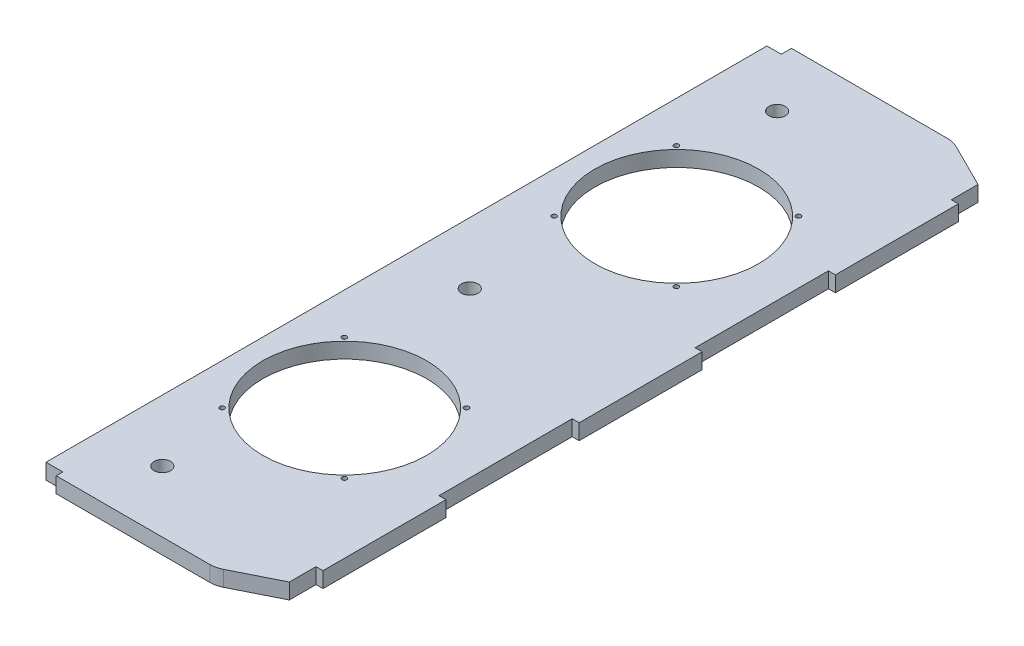
SolidWorks part; units mm, degrees
material "PE High Density"
ref_plane "Front Plane" through (0, 0, 0) normal (0, 0, 1) x (1, 0, 0)
ref_plane "Top Plane" through (0, 0, 0) normal (0, 1, 0) x (1, 0, 0)
ref_plane "Right Plane" through (0, 0, 0) normal (1, 0, 0) x (0, 0, -1)
sketch "Sketch1" plane through (0, 0, 0) normal (0, 1, 0) x (1, 0, 0)
  line L0 (0, 0) -> (0, 457.2)
  line L1 (0, 457.2) -> (139.7, 457.2)
  line L10 (139.7, 457.2) -> (139.7, 0)
  line L11 (139.7, 0) -> (0, 0)
  line L12 (0, 228.6) -> (139.7, 228.6) construction
  circle A0 centre (63.5, 125.73) radius 50.8
  circle A1 centre (38.1, 38.1) radius 5.08
  circle A3 centre (38.1, 419.1) radius 5.08
  circle A4 centre (63.5, 331.47) radius 50.8
  circle A5 centre (38.1, 228.6) radius 5.08
  dimension "D11" = 10.16
  dimension "D17" = 10.16
  dimension "D3" = 101.6
  dimension "D4" = 10.16
  dimension "D7" = 82.55
  dimension "D2" = 63.5
  dimension "Length of Rib" = 457.2
  dimension "D5" = 38.1
  dimension "D6" = 190.5
  dimension "D12" = 38.1
  dimension "D13" = 38.1
  dimension "D18" = 38.1
  dimension "D19" = 38.1
  dimension "Width of Rib" = 139.7
extrude "Boss-Extrude1" add sketch "Sketch1" along normal blind 9.652
sketch "Sketch4" plane through (0, 9.652, 0) normal (0, 1, 0) x (1, 0, 0)
  line L0 (10.4524, -8.5852) -> (10.4524, -21.2852) construction
  line L1 (0, 0) -> (10.4524, 0)
  line L2 (0, 0) -> (0, 4.1148)
  line L3 (0, 4.1148) -> (10.4524, 4.1148)
  line L4 (10.4524, 0) -> (10.4524, 4.1148)
  line L6 (0, 457.2) -> (8.8649, 457.2)
  line L7 (0, 457.2) -> (0, 450.85)
  line L8 (0, 450.85) -> (8.8649, 450.85)
  line L9 (8.8649, 457.2) -> (8.8649, 450.85)
extrude "Cut-Extrude1" cut sketch "Sketch4" against normal through all
chamfer "Chamfer1" distance 15.24 distance2 30.48 1 edges at (139.7, 4.826, -457.2)
chamfer "Chamfer2" distance 30.48 distance2 15.24 1 edges at (139.7, 4.826, 0)
fillet "Fillet2" radius 15.24 2 edges at (109.22, 4.826, -457.2) (109.22, 4.826, 0)
sketch "Sketch5" plane through (139.7, 0, 0) normal (1, 0, 0) x (0, 0, -1)
  line L0 (15.24, 9.652) -> (441.96, 9.652) construction
  line L1 (31.75, 9.652) -> (107.95, 9.652)
  line L2 (31.75, 9.652) -> (31.75, 0)
  line L3 (31.75, 0) -> (107.95, 0)
  line L4 (107.95, 9.652) -> (107.95, 0)
  line L5 (15.24, 0) -> (441.96, 0) construction
  line L6 (0, 0) -> (0, 9.652) construction
  line L7 (190.5, 9.652) -> (190.5, 0)
  line L8 (190.5, 9.652) -> (266.7, 9.652)
  line L9 (190.5, 0) -> (266.7, 0)
  line L10 (266.7, 9.652) -> (266.7, 0)
  line L11 (349.25, 9.652) -> (349.25, 0)
  line L12 (349.25, 9.652) -> (425.45, 9.652)
  line L13 (349.25, 0) -> (425.45, 0)
  line L14 (425.45, 9.652) -> (425.45, 0)
  dimension "D1" = 31.75
  dimension "D2" = 76.2
  dimension "D3" = 3
extrude "Boss-Extrude2" add sketch "Sketch5" along normal blind 4.318
sketch "Sketch7" plane through (0, 9.652, 0) normal (0, 1, 0) x (1, 0, 0)
  line L0 (10.4524, 0) -> (105.6223, 0) construction
  line L1 (139.7, 107.95) -> (139.7, 190.5) construction
  line L2 (101.092, 87.884) -> (101.092, 163.576) construction
  line L4 (101.092, 87.884) -> (25.4, 87.884) construction
  line L5 (25.4, 87.884) -> (25.4, 163.576) construction
  line L6 (25.4, 163.576) -> (101.092, 163.576) construction
  point P0 (101.092, 87.884)
  point P2 (25.4, 87.884)
  point P4 (25.4, 163.576)
  point P6 (101.092, 163.576)
  dimension "D1" = 87.884
  dimension "D2" = 38.608
  dimension "D3" = 75.692
  dimension "D4" = 75.692
  dimension "D5" = 75.692
  dimension "D6" = 75.692
hole_wizard "Ø3.0 (3) Diameter Hole1" positions "Sketch7" profile "Sketch8" hole size "Ø3.0" standard "ANSI Metric" end condition up to next
sketch "Sketch8" plane through (101.092, 9.652, -87.884) normal (1, 0, 0) x (0, 0, 1)
  line L0 (0, 0) -> (0, 9.652)
  line L1 (0, 9.652) -> (1.5, 9.652)
  line L2 (1.5, 9.652) -> (1.5, 0)
  line L5 (1.5, 0) -> (0, 0)
  line L11 (0, -6.35) -> (0, 107.95) construction
  dimension "Thru Hole Dia." = 3
  dimension "Thru Hole Depth" = 9.652
sketch "Sketch9" plane through (0, 9.652, 0) normal (0, 1, 0) x (1, 0, 0)
  line L0 (144.018, 228.6) -> (-0.0043, 228.6) construction
  line L1 (144.018, 266.7) -> (144.018, 190.5) construction
ref_plane "Plane1" through (0, 0, -228.6) normal (0, 0, 1) x (1, 0, 0)
mirror "Mirror1" about plane through (0, 0, -228.6) normal (0, 0, 1) of "Ø3.0 (3) Diameter Hole1"
